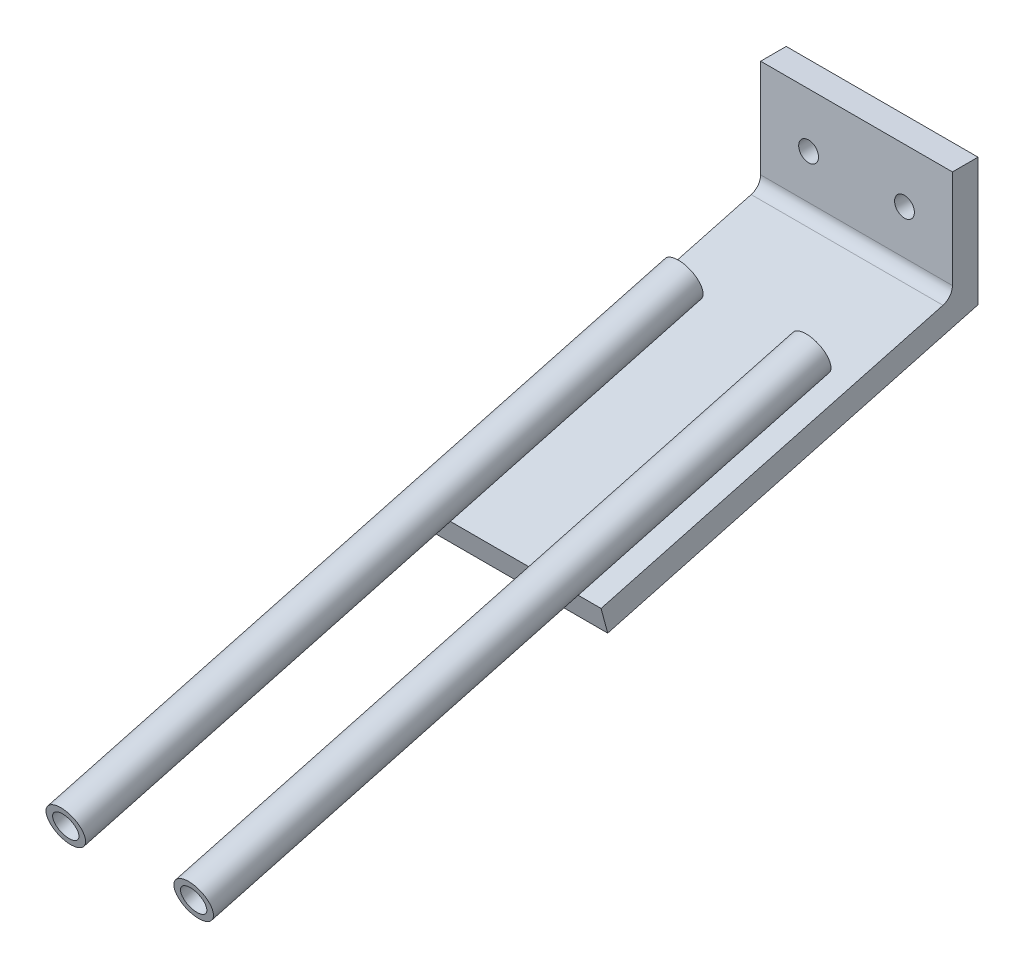
SolidWorks part; units mm, degrees
ref_plane "Front Plane" through (0, 0, 0) normal (1, 0, 0) x (0, 1, 0)
ref_plane "Top Plane" through (0, 0, 0) normal (0, 0, 1) x (0, 1, 0)
ref_plane "Right Plane" through (0, 0, 0) normal (0, 1, 0) x (-1, 0, 0)
sketch "Sketch1" plane through (0, 0, 0) normal (1, 0, 0) x (0, 1, 0)
  line L0 (-11.6568, 58.9586) -> (3.0693, 4)
  line L1 (3.0693, 4) -> (20, 4)
  line L2 (20, 4) -> (20, 0)
  line L3 (20, 0) -> (0, 0)
  line L4 (0, 0) -> (-15.5205, 57.9233)
  line L5 (-15.5205, 57.9233) -> (-11.6568, 58.9586)
  point P9 (-13.5887, 58.441)
  dimension "D1" = 4
  dimension "D2" = 4
  dimension "D3" = 75
  dimension "D4" = 20
  dimension "D5" = 60
extrude "Boss-Extrude1" add sketch "Sketch1" along normal mid plane 30
ref_plane "Plane1" through (0, -15.5205, 57.9233) normal (0, 0.2588, -0.9659) x (-1, 0, 0)
sketch "Sketch2" plane through (0, -15.5205, 57.9233) normal (0, 0.2588, -0.9659) x (-1, 0, 0)
  line L5 (-10, 7) -> (10, 7) construction
  line L6 (-15, 4) -> (15, 4) construction
  circle A0 centre (-10, 7) radius 2
  circle A1 centre (10, 7) radius 2
  circle A2 centre (-10, 7) radius 3
  circle A3 centre (10, 7) radius 3
  point P4 (0, 7)
  dimension "D1" = 4
  dimension "D2" = 6
  dimension "D3" = 20
extrude "Boss-Extrude2" add sketch "Sketch2" along normal offset from surface 40 and the other way blind 60 separate body up to face at (0, -13.5887, 58.441)
sketch "Sketch4" plane through (0, 0, 4) normal (0, 0, 1) x (1, 0, 0)
  line L0 (-7.5, 11.5347) -> (7.5, 11.5347) construction
  line L1 (15, 20) -> (15, 3.0693) construction
  circle A0 centre (-7.5, 11.5347) radius 1.55
  circle A1 centre (7.5, 11.5347) radius 1.55
  point P4 (0, 11.5347)
  point P8 (15, 11.5347)
  dimension "D1" = 3.1
  dimension "D3" = 15
extrude "Cut-Extrude1" cut sketch "Sketch4" against normal through all
fillet "Fillet1" radius 2 1 edges at (0, 3.0693, 4)
